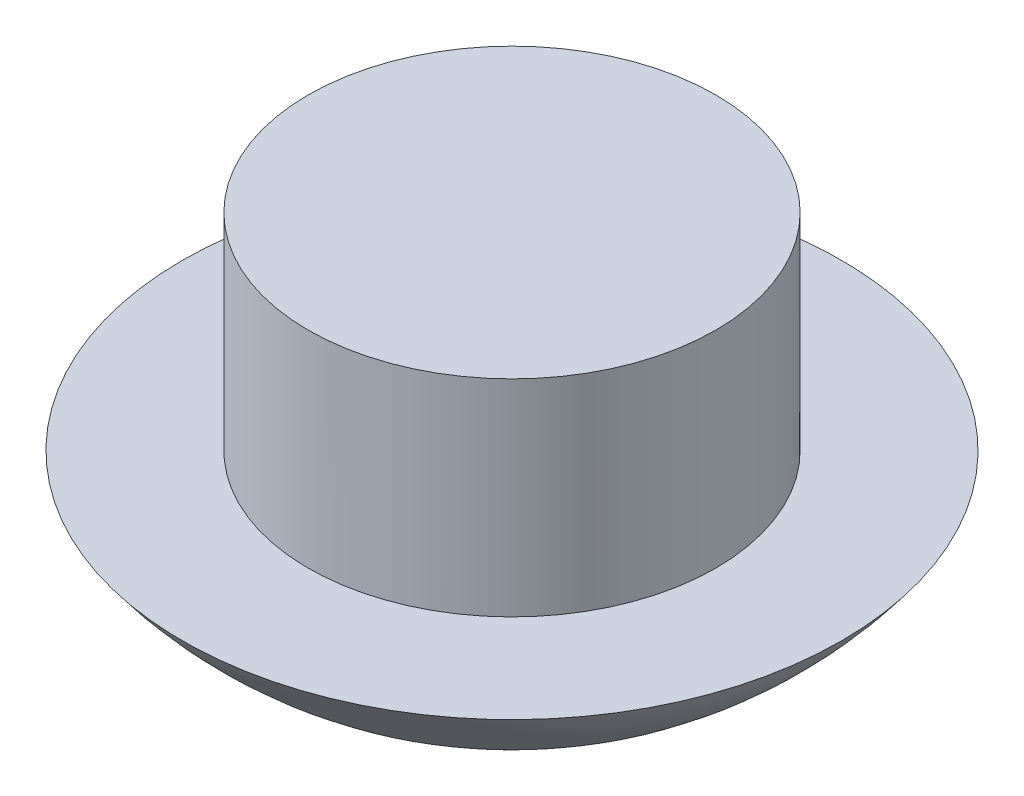
SolidWorks part; units mm, degrees
ref_plane "Front Plane" through (0, 0, 0) normal (0, 0, 1) x (1, 0, 0)
ref_plane "Top Plane" through (0, 0, 0) normal (0, 1, 0) x (1, 0, 0)
ref_plane "Right Plane" through (0, 0, 0) normal (1, 0, 0) x (0, 0, -1)
sketch "Sketch1" plane through (0, 0, 0) normal (0, 0, 1) x (1, 0, 0)
  line L0 (-10.795, 0) -> (10.795, 0)
  line L1 (0, -21.59) -> (0, 49000) construction
  line L10 (10.795, 0) -> (10.795, -12.7)
  line L11 (10.795, -12.7) -> (17.4596, -12.7)
  line L12 (-10.795, -12.7) -> (-17.4596, -12.7)
  line L19 (-10.795, 0) -> (-10.795, -12.7)
  arc A0 (-17.4596, -12.7) -> (17.4596, -12.7) centre (0, 0) ccw
  point P6 (0, 0)
  point P7 (0, 0)
  dimension "D1" = 43.18
  dimension "D2" = 21.59
  dimension "D3" = 6.6646
  dimension "D4" = 6.6646
revolve "Revolve5" add sketch "Sketch1" angle 360 about L1
sketch "Sketch2" plane through (0, 0, 0) normal (0, 1, 0) x (1, 0, 0)
  circle A0 centre (0, 0) radius 10.795
  dimension "D1" = 21.59
extrude "Cut-Extrude1" cut sketch "Sketch2" against normal blind 1.778
